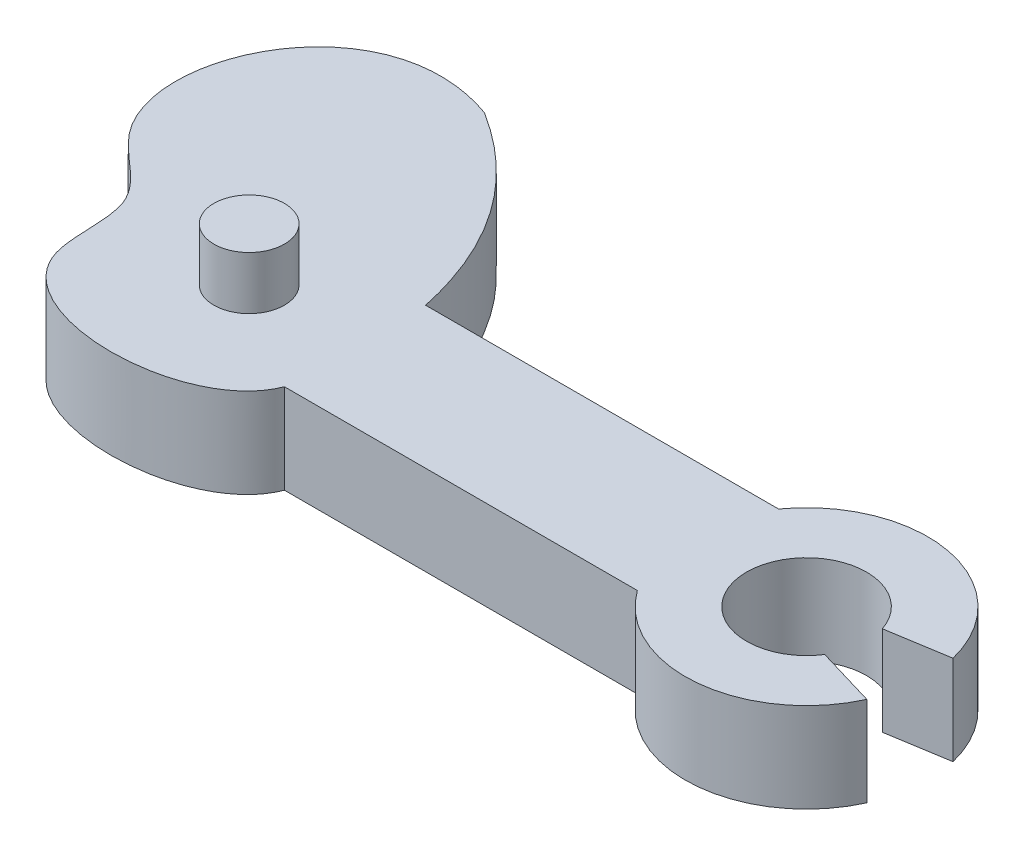
SolidWorks part; units mm, degrees
ref_plane "Front Plane" through (0, 0, 0) normal (0, 0, 1) x (1, 0, 0)
ref_plane "Top Plane" through (0, 0, 0) normal (0, 1, 0) x (1, 0, 0)
ref_plane "Right Plane" through (0, 0, 0) normal (1, 0, 0) x (0, 0, -1)
sketch "Sketch1" plane through (0, 0, 0) normal (0, 1, 0) x (1, 0, 0)
  line L0 (0, 0) -> (10, 0) construction
  line L1 (10, 0) -> (12.794, 0)
  line L2 (0, 0) -> (10, 0) construction
  line L3 (10, -2) -> (10, 2)
  line L4 (16.1332, 0.8101) -> (14.4086, 0.5319)
  line L5 (10, -2) -> (0, -2)
  line L6 (10, -2) -> (10, 2)
  line L7 (10, 2) -> (0, 2)
  line L8 (0, -2) -> (0, 2)
  line L9 (-6.5043, -2) -> (-0.5043, 2.6) construction
  line L10 (0, -2) -> (-6.5043, -2) construction
  line L11 (15.9224, -1.4212) -> (14.2261, -0.916)
  circle A0 centre (-3.5043, 0.3) radius 1 construction
  circle A1 centre (12.794, 0) radius 3.406 construction
  arc A2 (10, 2) -> (16.1332, 0.8101) centre (12.794, 0) cw
  arc A3 (10, -2) -> (15.9224, -1.4212) centre (12.794, 0) ccw
  circle A4 centre (12.794, 0) radius 1.7 construction
  arc A5 (14.2261, -0.916) -> (14.4169, 0.506) centre (12.794, 0) cw
  spline S0 degree 3 poles (0, -2) (-0.807, -4.0986) (-7.3608, -4.1963) (-6.3435, 0.5483) (-10.7782, 2.929) (-8.0517, 9.0455) (-3.8921, 7.5585) knots 0 0 0 0 0.35586 0.470048 0.583543 1 1 1 1
  spline S1 degree 2 poles (-3.8921, 7.5585) (-0.7715, 5.6017) (0, 2) knots 0 0 0 1 1 1
  point P6 (10, 0)
  dimension "D7" = 2
  dimension "D3" = 6.812
  dimension "D5" = 3.4
  dimension "D1" = 10
  dimension "D2" = 2.794
  dimension "D4" = 4
  dimension "D6" = 6
  dimension "D8" = 1.7468
extrude "Boss-Extrude2" add sketch "Sketch1" along normal blind 2.54 contours S1 S0 L8 | L8 L5 L3 L7 | L11 A5 L1 L3 A3 | L1 A5 L4 A2 L3
ref_plane "Plane1" through (0, 2.54, 0) normal (0, 1, 0) x (1, 0, 0)
sketch "Sketch3" plane through (0, 2.54, 0) normal (0, 1, 0) x (1, 0, 0)
  line L0 (0, 0) -> (-3, 0)
  circle A0 centre (-3, 0) radius 1
  dimension "D2" = 2
  dimension "D1" = 3
extrude "Boss-Extrude3" add sketch "Sketch3" along normal blind 1.5
ref_plane "Plane2" through (0, 0, 0) normal (0, -1, 0) x (-1, 0, 0)
sketch "Sketch4" plane through (0, 0, 0) normal (0, -1, 0) x (-1, 0, 0)
  line L0 (0, 0) -> (4.8724, 3.5013) construction
  line L2 (0, 0) -> (4.8724, 0) construction
  circle A0 centre (4.8724, 3.5013) radius 1
  dimension "D4" = 2
  dimension "D1" = 6
  dimension "D2" = 3.5013
  dimension "D3" = 35.701
extrude "Boss-Extrude5" add sketch "Sketch4" along normal blind 1.5 contours A0
